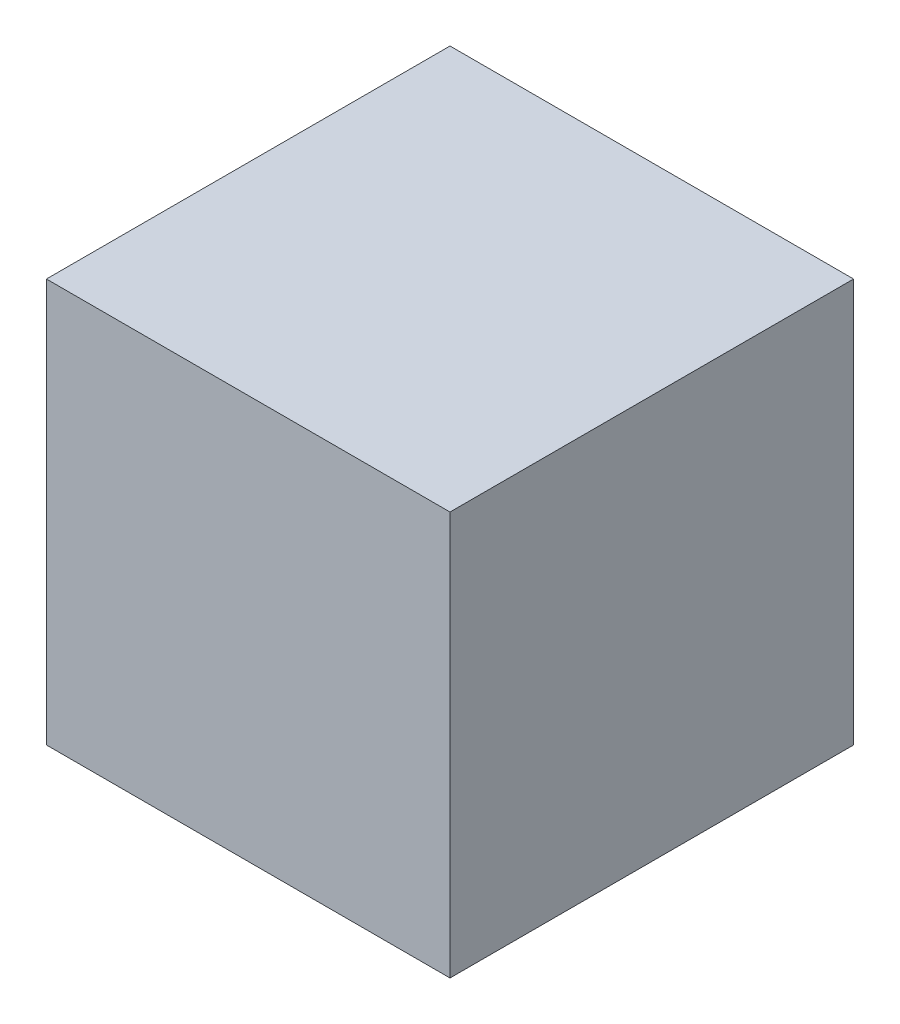
SolidWorks part; units mm, degrees
ref_plane "Front Plane" through (0, 0, 0) normal (0, 0, 1) x (1, 0, 0)
ref_plane "Top Plane" through (0, 0, 0) normal (0, 1, 0) x (1, 0, 0)
ref_plane "Right Plane" through (0, 0, 0) normal (1, 0, 0) x (0, 0, -1)
sketch "Sketch1" plane through (0, 0, 0) normal (0, 1, 0) x (1, 0, 0)
  line L1 (-5, -5) -> (5, -5)
  line L2 (-5, -5) -> (-5, 5)
  line L3 (-5, 5) -> (5, 5)
  line L4 (5, -5) -> (5, 5)
  line L5 (-5, -5) -> (5, 5) construction
  line L6 (-5, 5) -> (5, -5) construction
  point P0 (0, 0)
  dimension "D1" = 10
extrude "Boss-Extrude1" add sketch "Sketch1" along normal blind 10
